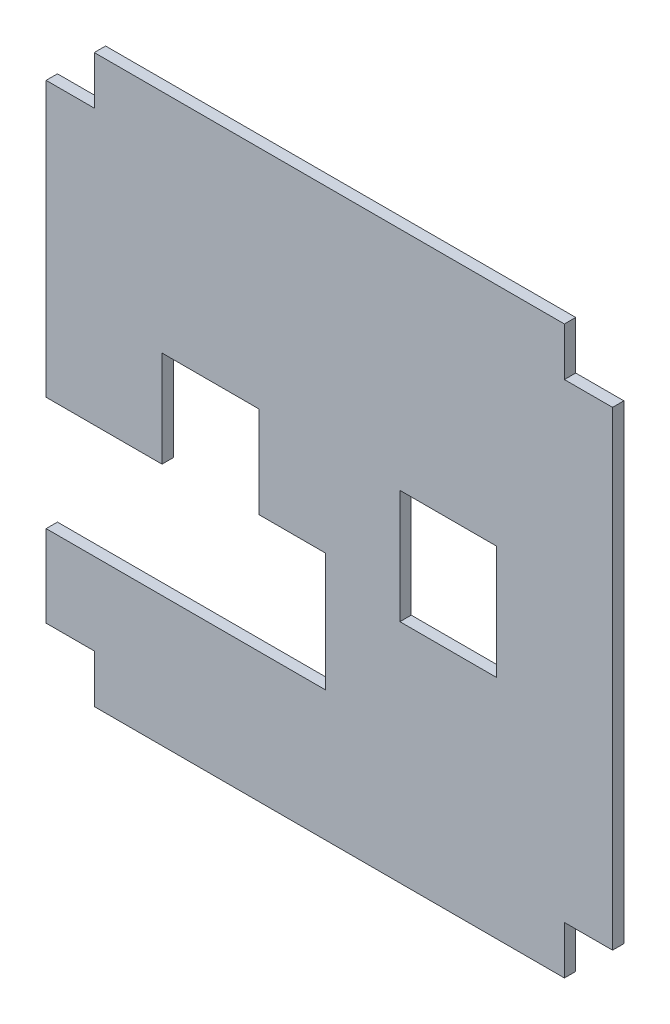
SolidWorks part; units mm, degrees
ref_plane "Front Plane" through (0, 0, 0) normal (0, 0, 1) x (1, 0, 0)
ref_plane "Top Plane" through (0, 0, 0) normal (0, 1, 0) x (1, 0, 0)
ref_plane "Right Plane" through (0, 0, 0) normal (1, 0, 0) x (0, 0, -1)
sketch "Sketch1" plane through (0, 0, 0) normal (0, 0, 1) x (1, 0, 0)
  line L0 (-158.2257, -298.7763) -> (-158.2257, -313.2363)
  line L1 (-122.1857, -298.7763) -> (-108.8639, -298.7763)
  line L2 (-108.8639, -298.7763) -> (-108.8639, -281.7763)
  line L4 (-120.6857, -277.8561) -> (-108.8639, -277.8561)
  line L5 (-108.8639, -277.8561) -> (-108.8639, -281.7763)
  line L36 (-158.2257, -278.6963) -> (-137.7657, -278.6963)
  line L38 (-122.1857, -298.7763) -> (-158.2257, -298.7763)
  line L52 (-66.7257, -321.7363) -> (-66.7257, -313.2363)
  line L53 (-149.7257, -321.7363) -> (-66.7257, -321.7363)
  line L54 (-149.7257, -313.2363) -> (-149.7257, -321.7363)
  line L55 (-158.2257, -313.2363) -> (-149.7257, -313.2363)
  line L56 (-158.2257, -230.2363) -> (-158.2257, -278.6963)
  line L57 (-149.7257, -230.2363) -> (-158.2257, -230.2363)
  line L58 (-149.7257, -221.7363) -> (-149.7257, -230.2363)
  line L59 (-66.7257, -221.7363) -> (-149.7257, -221.7363)
  line L70 (-66.7257, -230.2363) -> (-66.7257, -221.7363)
  line L71 (-58.2257, -230.2363) -> (-66.7257, -230.2363)
  line L72 (-58.2257, -313.2363) -> (-58.2257, -230.2363)
  line L73 (-66.7257, -313.2363) -> (-58.2257, -313.2363)
  line L161 (-95.7657, -261.6963) -> (-95.7657, -281.7763)
  line L162 (-78.6857, -261.6963) -> (-95.7657, -261.6963)
  line L163 (-78.6857, -281.7763) -> (-78.6857, -261.6963)
  line L164 (-95.7657, -281.7763) -> (-78.6857, -281.7763)
  line L179 (-120.6857, -277.8561) -> (-120.6857, -261.6963)
  line L180 (-120.6857, -261.6963) -> (-137.7657, -261.6963)
  line L181 (-137.7657, -261.6963) -> (-137.7657, -278.6963)
extrude "Boss-Extrude1" add sketch "Sketch1" along normal blind 2
